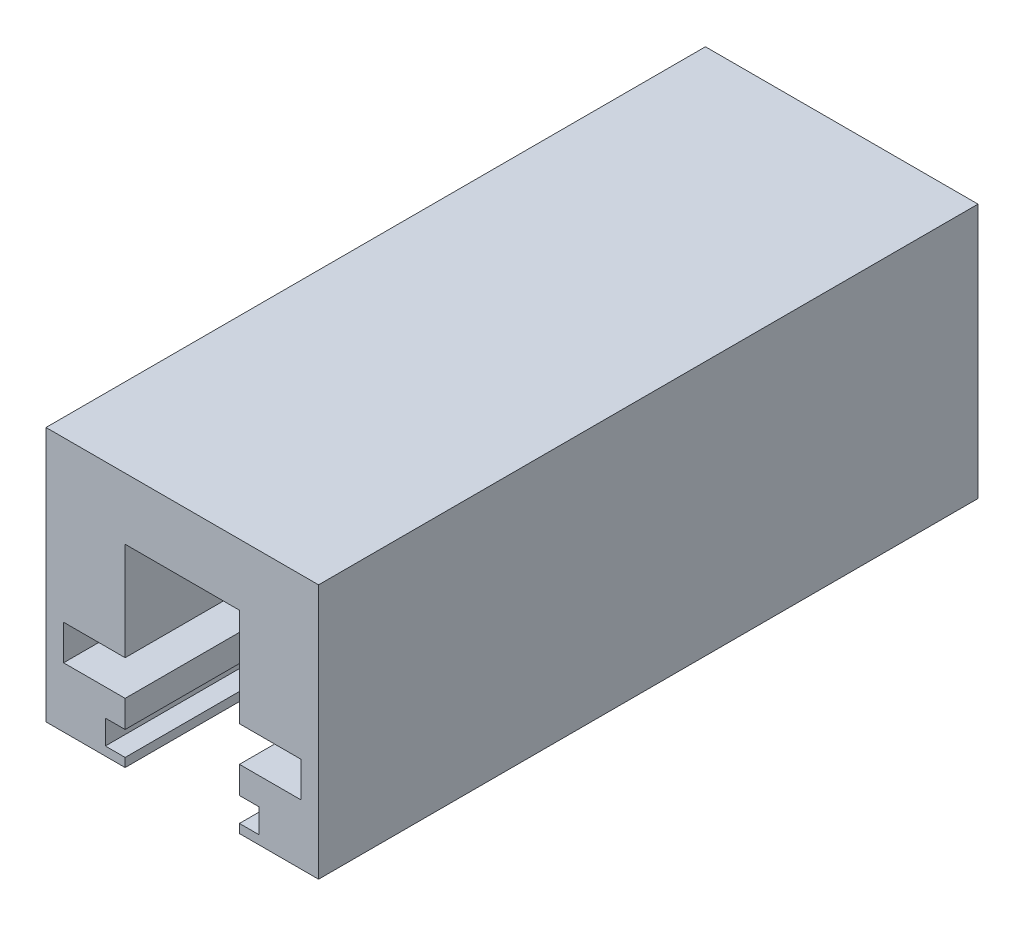
SolidWorks part; units mm, degrees
ref_plane "Front Plane" through (0, 0, 0) normal (0, 0, 1) x (1, 0, 0)
ref_plane "Top Plane" through (0, 0, 0) normal (0, 1, 0) x (1, 0, 0)
ref_plane "Right Plane" through (0, 0, 0) normal (1, 0, 0) x (0, 0, -1)
sketch "Sketch1" plane through (0, 0, 0) normal (0, 0, 1) x (1, 0, 0)
  line L0 (-31, 0) -> (-31, 29)
  line L1 (-31, 29) -> (0, 29)
  line L2 (0, 29) -> (0, 0)
  line L3 (0, 0) -> (-9, 0)
  line L4 (-9, 0) -> (-9, 22)
  line L5 (-9, 22) -> (-22, 22)
  line L6 (-22, 22) -> (-22, 0)
  line L7 (-22, 0) -> (-31, 0)
  line L8 (-22, 1) -> (-24.25, 1)
  line L9 (-24.25, 1) -> (-24.25, 3.75)
  line L10 (-24.25, 3.75) -> (-22, 3.75)
  line L11 (-22, 6.82) -> (-29, 6.82)
  line L12 (-29, 6.82) -> (-29, 10.82)
  line L13 (-29, 10.82) -> (-22, 10.82)
  line L14 (-9, 1) -> (-6.75, 1)
  line L15 (-6.75, 1) -> (-6.75, 3.75)
  line L16 (-6.75, 3.75) -> (-9, 3.75)
  line L17 (-9, 6.82) -> (-2, 6.82)
  line L18 (-2, 6.82) -> (-2, 10.82)
  line L19 (-2, 10.82) -> (-9, 10.82)
  line L20 (-22, 0) -> (-21.75, 0)
  line L21 (-21.75, 0) -> (-21.75, 1)
  line L22 (-21.75, 1) -> (-22, 1)
  line L23 (-9, 0) -> (-9.25, 0)
  line L24 (-9.25, 0) -> (-9.25, 1)
  line L25 (-9.25, 1) -> (-9, 1)
  dimension "D1" = 31
  dimension "D2" = 9
  dimension "D3" = 29
  dimension "D4" = 7
  dimension "D5" = 1
  dimension "D6" = 2.75
  dimension "D7" = 3.07
  dimension "D8" = 4
  dimension "D9" = 2.25
  dimension "D10" = 7
  dimension "D11" = 1
  dimension "D12" = 3.07
  dimension "D13" = 0
  dimension "D14" = 0.25
extrude "Boss-Extrude2" add sketch "Sketch1" along normal blind 75 contours L19 L18 L17 L4 L16 L15 L14 L3 L2 L1 L0 L7 L6 L8 L9 L10 L11 L12 L13 L5
